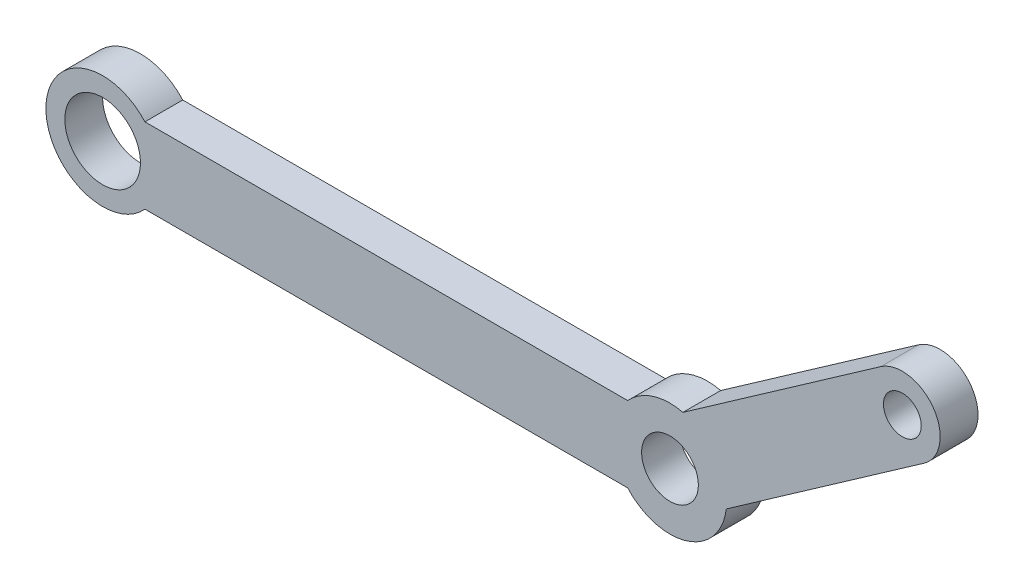
SolidWorks part; units mm, degrees
ref_plane "前视基准面" through (0, 0, 0) normal (0, 0, 1) x (1, 0, 0)
ref_plane "上视基准面" through (0, 0, 0) normal (0, 1, 0) x (1, 0, 0)
ref_plane "右视基准面" through (0, 0, 0) normal (1, 0, 0) x (0, 0, -1)
sketch "草图1" plane through (0, 0, 0) normal (0, 0, 1) x (1, 0, 0)
  line L1 (41.1401, 10.242) -> (30.6845, 2.9209)
  line L2 (43.4344, 6.9653) -> (32.9788, -0.3557)
  line L3 (2.2361, -2) -> (27.7639, -2)
  line L4 (2.2361, 2) -> (27.7639, 2)
  arc A0 (43.4344, 6.9653) -> (41.1401, 10.242) centre (42.2873, 8.6036) ccw
  arc A1 (30.6845, 2.9209) -> (27.7639, 2) centre (30, 0) ccw
  arc A2 (2.2361, 2) -> (2.2361, -2) centre (0, 0) ccw
  arc A3 (27.7639, -2) -> (32.9788, -0.3557) centre (30, 0) ccw
  dimension "D1" = 4
  dimension "D2" = 6
extrude "凸台-拉伸1" add sketch "草图1" along normal blind 2
sketch "草图2" plane through (0, 0, 2) normal (0, 0, 1) x (1, 0, 0)
  circle A0 centre (0, 0) radius 2
  circle A1 centre (30, 0) radius 1.5
  circle A2 centre (42.2873, 8.6036) radius 1
  arc A3 (27.7639, -2) -> (32.9788, -0.3557) centre (30, 0) ccw construction
  dimension "D1" = 4
  dimension "D2" = 3
  dimension "D3" = 2
extrude "切除-拉伸1" cut sketch "草图2" against normal blind 2
